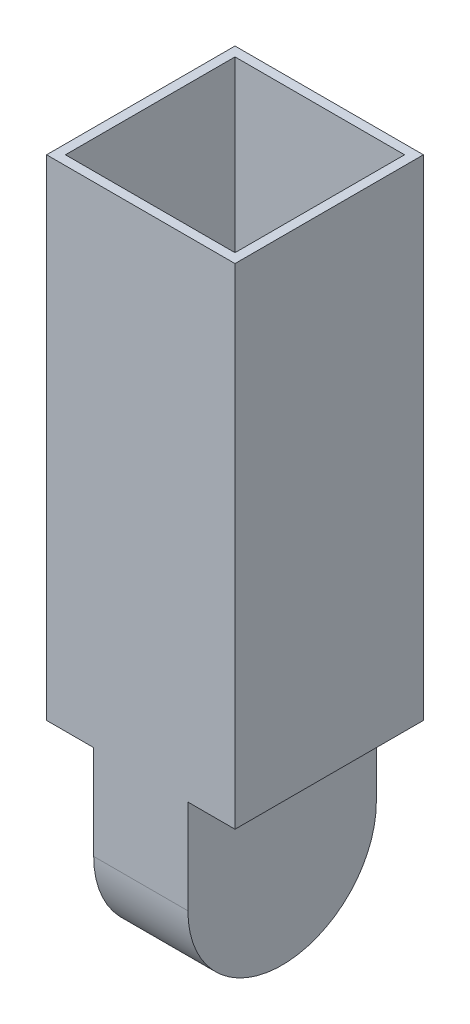
SolidWorks part; units mm, degrees
ref_plane "Front" through (0, 0, 0) normal (0, 0, 1) x (1, 0, 0)
ref_plane "Top" through (0, 0, 0) normal (0, 1, 0) x (1, 0, 0)
ref_plane "Right" through (0, 0, 0) normal (1, 0, 0) x (0, 0, -1)
sketch "草图1" plane through (0, 0, 0) normal (0, 1, 0) x (1, 0, 0)
  line L1 (-10, 10) -> (10, 10)
  line L2 (-10, 10) -> (-10, -10)
  line L3 (-10, -10) -> (10, -10)
  line L4 (10, 10) -> (10, -10)
  line L5 (-9, 9) -> (9, 9)
  line L6 (-9, 9) -> (-9, -9)
  line L7 (-9, -9) -> (9, -9)
  line L8 (9, 9) -> (9, -9)
  dimension "D1" = 20
  dimension "D2" = 20
  dimension "D3" = 10
  dimension "D4" = 10
  dimension "D5" = 18
  dimension "D6" = 18
  dimension "D7" = 9
  dimension "D8" = 9
extrude "凸台-拉伸1" add sketch "草图1" along normal blind 50
sketch "草图2" plane through (0, 0, 0) normal (0, -1, 0) x (1, 0, 0)
  line L1 (-10, 10) -> (10, 10)
  line L2 (-10, 10) -> (-10, -10)
  line L3 (-10, -10) -> (10, -10)
  line L4 (10, 10) -> (10, -10)
extrude "凸台-拉伸2" add sketch "草图2" along normal blind 2
sketch "草图6" plane through (0, 0, 0) normal (1, 0, 0) x (0, 0, -1)
  line L0 (10, -2) -> (-10, -2) construction
  line L1 (-10, -2) -> (10, -2)
  line L3 (-10, -12) -> (-10, -2)
  line L5 (10, -12) -> (10, -2)
  arc A0 (-10, -12) -> (10, -12) centre (0, -12) ccw
  dimension "D1" = 10
extrude "凸台-拉伸3" add sketch "草图6" along normal mid plane 10
